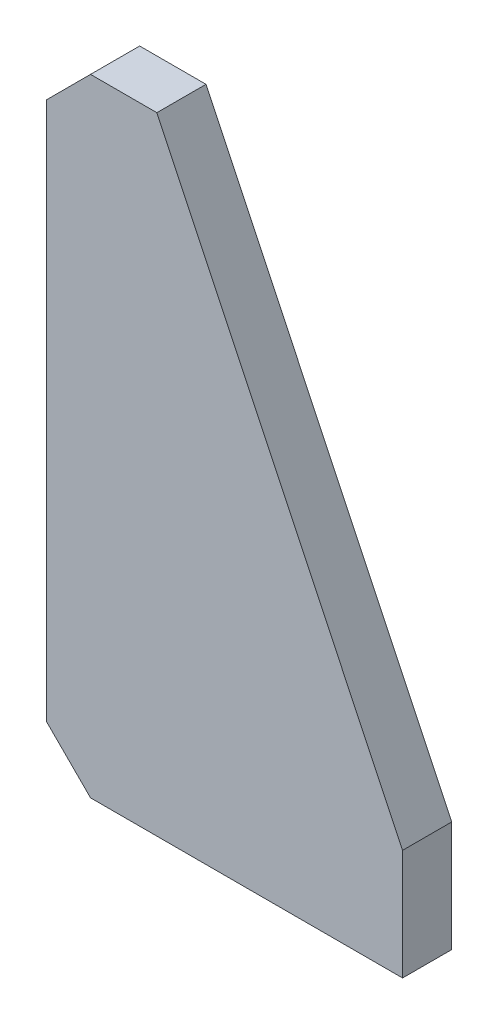
SolidWorks part; units mm, degrees
ref_plane "Спереди" through (0, 0, 0) normal (0, 0, 1) x (1, 0, 0)
ref_plane "Сверху" through (0, 0, 0) normal (0, 1, 0) x (1, 0, 0)
ref_plane "Справа" through (0, 0, 0) normal (1, 0, 0) x (0, 0, -1)
sketch "Эскиз1" plane through (0, 0, 0) normal (0, 0, 1) x (1, 0, 0)
  line L0 (0, 0) -> (0, 45)
  line L1 (0, 45) -> (-100, 255)
  line L2 (-100, 255) -> (-127, 255)
  line L3 (-145, 237) -> (-145, 0)
  line L4 (-145, 0) -> (0, 0)
  line L5 (-127, 255) -> (-145, 237)
extrude "Бобышка-Вытянуть1" add sketch "Эскиз1" along normal blind 20 contours L3 L4 L0 L1 L2 L5
chamfer "Фаска1" distance 18 angle 45 1 edges at (-145, 0, 10)
